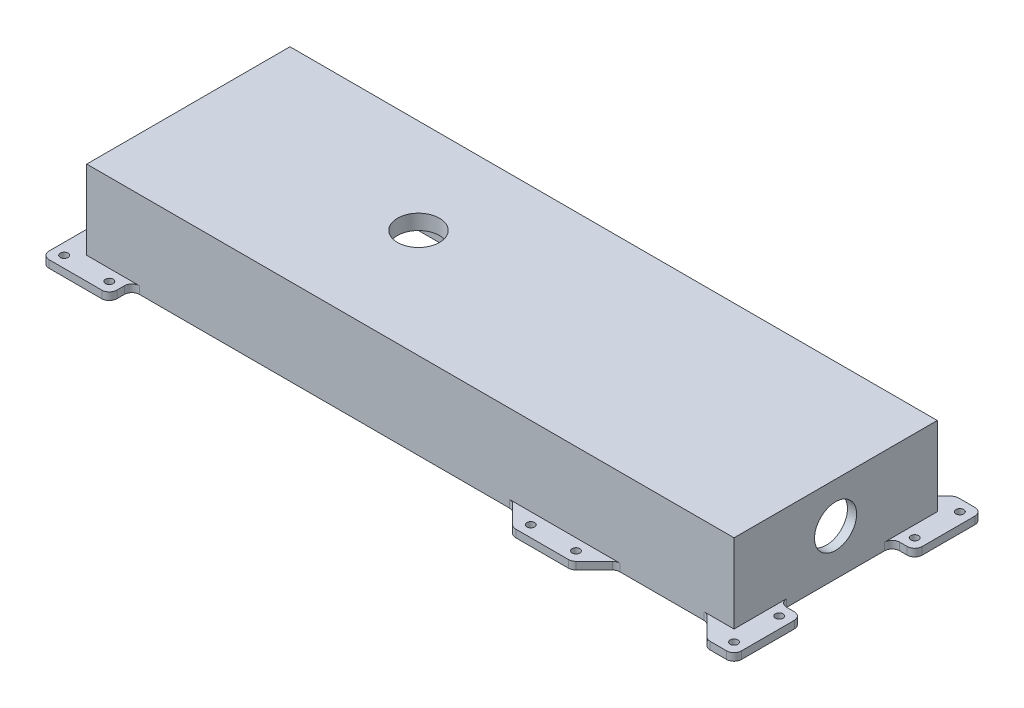
SolidWorks part; units mm, degrees
material "6061 Alloy"
ref_plane "Front Plane" through (0, 0, 0) normal (0, 0, 1) x (1, 0, 0)
ref_plane "Top Plane" through (0, 0, 0) normal (0, 1, 0) x (1, 0, 0)
ref_plane "Right Plane" through (0, 0, 0) normal (1, 0, 0) x (0, 0, -1)
sketch "Sketch1" plane through (0, 0, 0) normal (0, 1, 0) x (1, 0, 0)
  line L1 (-273.05, -85.725) -> (273.05, -85.725)
  line L2 (-273.05, -85.725) -> (-273.05, 85.725)
  line L3 (-273.05, 85.725) -> (273.05, 85.725)
  line L4 (273.05, -85.725) -> (273.05, 85.725)
  line L5 (-273.05, -85.725) -> (273.05, 85.725) construction
  line L6 (-273.05, 85.725) -> (273.05, -85.725) construction
  point P0 (0, 0)
  dimension "D1" = 546.1
  dimension "D2" = 171.45
extrude "Boss-Extrude1" add sketch "Sketch1" along normal blind 73.025
sketch "Sketch2" plane through (0, 0, 0) normal (0, -1, 0) x (1, 0, 0)
  line L0 (-220.7486, -78.0129) -> (-220.7486, -85.725) construction
  line L1 (273.05, -85.725) -> (-273.05, -85.725) construction
  line L2 (-265.3379, -33.4236) -> (-273.05, -33.4236) construction
  line L3 (-273.05, -85.725) -> (-273.05, 85.725) construction
  line L4 (220.7486, -78.0129) -> (220.7486, -85.725) construction
  line L5 (265.3379, -33.4236) -> (273.05, -33.4236) construction
  line L6 (273.05, 85.725) -> (273.05, -85.725) construction
  line L7 (-220.7486, 78.0129) -> (-220.7486, 85.725) construction
  line L8 (-273.05, 85.725) -> (273.05, 85.725) construction
  line L9 (-265.3379, 33.4236) -> (-273.05, 33.4236) construction
  line L10 (265.3379, 33.4236) -> (273.05, 33.4236) construction
  line L11 (220.7486, 78.0129) -> (220.7486, 85.725)
  line L18 (220.7486, 78.0129) -> (-220.7486, 78.0129)
  line L19 (265.3379, -33.4236) -> (265.3379, 33.4236)
  line L20 (-220.7486, -78.0129) -> (220.7486, -78.0129)
  line L21 (-265.3379, 33.4236) -> (-265.3379, -33.4236)
  arc A0 (265.3379, -33.4236) -> (220.7486, -78.0129) centre (220.7486, -33.4236) cw
  arc A1 (220.7486, 78.0129) -> (265.3379, 33.4236) centre (220.7486, 33.4236) cw
  arc A2 (-220.7486, 78.0129) -> (-265.3379, 33.4236) centre (-220.7486, 33.4236) ccw
  arc A3 (-220.7486, -78.0129) -> (-265.3379, -33.4236) centre (-220.7486, -33.4236) cw
  dimension "D2" = 44.5893
extrude "Cut-Extrude1" cut sketch "Sketch2" against normal offset from surface (60.325 mm away) 12.7 contours A1 L19 A0 L20 A3 L21 A2 L18 up to face at (0, 73.025, 0)
sketch "Sketch4" plane through (0, 60.325, 0) normal (0, -1, 0) x (1, 0, 0)
  line L0 (-265.3379, -6.35) -> (-265.3379, 6.35)
  line L2 (-265.3379, 33.4236) -> (-265.3379, -33.4236) construction
  line L3 (-265.3379, 6.35) -> (-96.9126, 6.35)
  line L4 (-96.9126, 6.35) -> (-96.9126, 78.0129)
  line L5 (-220.7486, 78.0129) -> (220.7486, 78.0129) construction
  line L6 (-96.9126, 78.0129) -> (-84.2126, 78.0129)
  line L7 (-84.2126, 78.0129) -> (-84.2126, 6.35)
  line L8 (-84.2126, 6.35) -> (84.2126, 6.35)
  line L9 (84.2126, 6.35) -> (84.2126, 78.0129)
  line L10 (84.2126, 78.0129) -> (96.9126, 78.0129)
  line L11 (96.9126, 78.0129) -> (96.9126, 6.35)
  line L12 (96.9126, 6.35) -> (265.3379, 6.35)
  line L13 (265.3379, 33.4236) -> (265.3379, -33.4236) construction
  line L14 (265.3379, 6.35) -> (265.3379, -6.35)
  line L15 (265.3379, -6.35) -> (96.9126, -6.35)
  line L16 (96.9126, -6.35) -> (96.9126, -78.0129)
  line L17 (220.7486, -78.0129) -> (-220.7486, -78.0129) construction
  line L18 (96.9126, -78.0129) -> (84.2126, -78.0129)
  line L19 (-220.7486, -78.0129) -> (220.7486, -78.0129) construction
  line L20 (84.2126, -78.0129) -> (84.2126, -6.35)
  line L21 (84.2126, -6.35) -> (-84.2126, -6.35)
  line L22 (-84.2126, -6.35) -> (-84.2126, -78.0129)
  line L23 (-84.2126, -78.0129) -> (-96.9126, -78.0129)
  line L24 (-96.9126, -78.0129) -> (-96.9126, -6.35)
  line L25 (-96.9126, -6.35) -> (-265.3379, -6.35)
  point P3 (-265.3379, 0)
  dimension "D1" = 12.7
extrude "Boss-Extrude3" [suppressed] add sketch "Sketch4" along normal blind 6.35
fillet "Fillet1" [suppressed] radius 19.05
sketch "Sketch5" plane through (0, 73.025, 0) normal (0, 1, 0) x (1, 0, 0)
  circle A0 centre (-84.7007, 5.8112) radius 17.7497
  circle A1 centre (-84.7007, 5.8112) radius 20.2897
  circle A2 centre (-84.7007, 5.8112) radius 20.2897 construction
  dimension "D1" = 0
  dimension "D2" = 2.54
extrude "Cut-Extrude2" cut sketch "Sketch5" against normal up to next
sketch "Sketch6" plane through (273.05, 0, 0) normal (1, 0, 0) x (0, 0, -1)
  circle A0 centre (-0.0776, 38.74) radius 17.7497
  circle A1 centre (-0.0776, 38.74) radius 20.2897
  circle A2 centre (-0.0776, 38.74) radius 20.2897 construction
  dimension "D1" = 0
  dimension "D2" = 2.54
extrude "Cut-Extrude3" cut sketch "Sketch6" against normal up to next
chamfer "Chamfer1" distance 0.635 8 edges at (252.278, 0, -64.953) (265.3379, 0, 0) (252.278, 0, 64.953) (0, 0, 78.0129) (-252.278, 0, 64.953) (0, 0, -78.0129) (-265.3379, 0, 0) (-252.278, 0, -64.953)
sketch "Sketch7" plane through (0, 0, 0) normal (0, -1, 0) x (1, 0, 0)
  line L0 (-273.05, -85.725) -> (-273.05, 85.725) construction
  line L1 (273.05, -85.725) -> (-273.05, -85.725) construction
  line L2 (273.05, 85.725) -> (273.05, -85.725) construction
  line L3 (-273.05, 85.725) -> (273.05, 85.725) construction
  line L4 (-273.05, -85.725) -> (-273.05, 85.725)
  line L5 (273.05, -85.725) -> (-273.05, -85.725)
  line L6 (273.05, 85.725) -> (273.05, -85.725)
  line L7 (-273.05, 85.725) -> (273.05, 85.725)
  line L36 (-228.6, -85.725) -> (83.6395, -85.725)
  line L37 (88.1296, -87.5849) -> (103.4599, -102.9151)
  line L38 (107.95, -104.775) -> (152.4, -104.775)
  line L39 (156.8901, -102.9151) -> (172.2204, -87.5849)
  line L40 (176.7105, -85.725) -> (247.65, -85.725)
  line L41 (252.1401, -87.5849) -> (267.4704, -102.9151)
  line L42 (271.9605, -104.775) -> (285.75, -104.775)
  line L43 (292.1, -98.425) -> (292.1, -53.975)
  line L44 (285.75, -47.625) -> (279.4, -47.625)
  line L45 (273.05, -41.275) -> (273.05, 41.275)
  line L46 (279.4, 47.625) -> (285.75, 47.625)
  line L47 (292.1, 53.975) -> (292.1, 98.425)
  line L48 (285.75, 104.775) -> (271.9605, 104.775)
  line L49 (267.4704, 102.9151) -> (252.1401, 87.5849)
  line L50 (247.65, 85.725) -> (176.7105, 85.725)
  line L51 (172.2204, 87.5849) -> (156.8901, 102.9151)
  line L52 (152.4, 104.775) -> (107.95, 104.775)
  line L53 (103.4599, 102.9151) -> (88.1296, 87.5849)
  line L54 (83.6395, 85.725) -> (-228.6, 85.725)
  line L55 (-234.95, 92.075) -> (-234.95, 98.425)
  line L56 (-241.3, 104.775) -> (-285.75, 104.775)
  line L57 (-292.1, 98.425) -> (-292.1, 53.975)
  line L58 (-285.75, 47.625) -> (-279.4, 47.625)
  line L59 (-273.05, 41.275) -> (-273.05, -41.275)
  line L60 (-279.4, -47.625) -> (-285.75, -47.625)
  line L61 (-292.1, -53.975) -> (-292.1, -98.425)
  line L62 (-285.75, -104.775) -> (-241.3, -104.775)
  line L63 (-234.95, -98.425) -> (-234.95, -92.075)
  line L64 (-228.6, -85.725) -> (83.6395, -85.725)
  line L65 (88.1296, -87.5849) -> (103.4599, -102.9151)
  line L66 (107.95, -104.775) -> (152.4, -104.775)
  line L67 (156.8901, -102.9151) -> (172.2204, -87.5849)
  line L68 (176.7105, -85.725) -> (247.65, -85.725)
  line L69 (252.1401, -87.5849) -> (267.4704, -102.9151)
  line L70 (271.9605, -104.775) -> (285.75, -104.775)
  line L71 (292.1, -98.425) -> (292.1, -53.975)
  line L72 (285.75, -47.625) -> (279.4, -47.625)
  line L73 (273.05, -41.275) -> (273.05, 41.275)
  line L74 (279.4, 47.625) -> (285.75, 47.625)
  line L75 (292.1, 53.975) -> (292.1, 98.425)
  line L76 (285.75, 104.775) -> (271.9605, 104.775)
  line L77 (267.4704, 102.9151) -> (252.1401, 87.5849)
  line L78 (247.65, 85.725) -> (176.7105, 85.725)
  line L79 (172.2204, 87.5849) -> (156.8901, 102.9151)
  line L80 (152.4, 104.775) -> (107.95, 104.775)
  line L81 (103.4599, 102.9151) -> (88.1296, 87.5849)
  line L82 (83.6395, 85.725) -> (-228.6, 85.725)
  line L83 (-234.95, 92.075) -> (-234.95, 98.425)
  line L84 (-241.3, 104.775) -> (-285.75, 104.775)
  line L85 (-292.1, 98.425) -> (-292.1, 53.975)
  line L86 (-285.75, 47.625) -> (-279.4, 47.625)
  line L87 (-273.05, 41.275) -> (-273.05, -41.275)
  line L88 (-279.4, -47.625) -> (-285.75, -47.625)
  line L89 (-292.1, -53.975) -> (-292.1, -98.425)
  line L90 (-285.75, -104.775) -> (-241.3, -104.775)
  line L91 (-234.95, -98.425) -> (-234.95, -92.075)
  circle A0 centre (111.125, 95.25) radius 3.2639 construction
  circle A1 centre (149.225, 95.25) radius 3.2639 construction
  circle A2 centre (282.575, 95.25) radius 3.2639 construction
  circle A3 centre (282.575, 57.15) radius 3.2639 construction
  circle A4 centre (282.575, -57.15) radius 3.2639 construction
  circle A5 centre (282.575, -95.25) radius 3.2639 construction
  circle A6 centre (149.225, -95.25) radius 3.2639 construction
  circle A7 centre (111.125, -95.25) radius 3.2639 construction
  circle A8 centre (-244.475, -95.25) radius 3.2639 construction
  circle A9 centre (-282.575, -95.25) radius 3.2639 construction
  circle A10 centre (-282.575, -57.15) radius 3.2639 construction
  circle A11 centre (-282.575, 57.15) radius 3.2639 construction
  circle A12 centre (-244.475, 95.25) radius 3.2639 construction
  circle A13 centre (-282.575, 95.25) radius 3.2639 construction
  circle A14 centre (111.125, 95.25) radius 3.2639
  circle A15 centre (149.225, 95.25) radius 3.2639
  circle A16 centre (282.575, 95.25) radius 3.2639
  circle A17 centre (282.575, 57.15) radius 3.2639
  circle A18 centre (282.575, -57.15) radius 3.2639
  circle A19 centre (282.575, -95.25) radius 3.2639
  circle A20 centre (149.225, -95.25) radius 3.2639
  circle A21 centre (111.125, -95.25) radius 3.2639
  circle A22 centre (-244.475, -95.25) radius 3.2639
  circle A23 centre (-282.575, -95.25) radius 3.2639
  circle A24 centre (-282.575, -57.15) radius 3.2639
  circle A25 centre (-282.575, 57.15) radius 3.2639
  circle A26 centre (-244.475, 95.25) radius 3.2639
  circle A27 centre (-282.575, 95.25) radius 3.2639
  arc A28 (-228.6, -85.725) -> (-234.95, -92.075) centre (-228.6, -92.075) ccw
  arc A29 (88.1296, -87.5849) -> (83.6395, -85.725) centre (83.6395, -92.075) ccw
  arc A30 (103.4599, -102.9151) -> (107.95, -104.775) centre (107.95, -98.425) ccw
  arc A31 (152.4, -104.775) -> (156.8901, -102.9151) centre (152.4, -98.425) ccw
  arc A32 (176.7105, -85.725) -> (172.2204, -87.5849) centre (176.7105, -92.075) ccw
  arc A33 (252.1401, -87.5849) -> (247.65, -85.725) centre (247.65, -92.075) ccw
  arc A34 (267.4704, -102.9151) -> (271.9605, -104.775) centre (271.9605, -98.425) ccw
  arc A35 (285.75, -104.775) -> (292.1, -98.425) centre (285.75, -98.425) ccw
  arc A36 (292.1, -53.975) -> (285.75, -47.625) centre (285.75, -53.975) ccw
  arc A37 (273.05, -41.275) -> (279.4, -47.625) centre (279.4, -41.275) ccw
  arc A38 (279.4, 47.625) -> (273.05, 41.275) centre (279.4, 41.275) ccw
  arc A39 (285.75, 47.625) -> (292.1, 53.975) centre (285.75, 53.975) ccw
  arc A40 (292.1, 98.425) -> (285.75, 104.775) centre (285.75, 98.425) ccw
  arc A41 (271.9605, 104.775) -> (267.4704, 102.9151) centre (271.9605, 98.425) ccw
  arc A42 (247.65, 85.725) -> (252.1401, 87.5849) centre (247.65, 92.075) ccw
  arc A43 (172.2204, 87.5849) -> (176.7105, 85.725) centre (176.7105, 92.075) ccw
  arc A44 (156.8901, 102.9151) -> (152.4, 104.775) centre (152.4, 98.425) ccw
  arc A45 (107.95, 104.775) -> (103.4599, 102.9151) centre (107.95, 98.425) ccw
  arc A46 (83.6395, 85.725) -> (88.1296, 87.5849) centre (83.6395, 92.075) ccw
  arc A47 (-234.95, 92.075) -> (-228.6, 85.725) centre (-228.6, 92.075) ccw
  arc A48 (-234.95, 98.425) -> (-241.3, 104.775) centre (-241.3, 98.425) ccw
  arc A49 (-285.75, 104.775) -> (-292.1, 98.425) centre (-285.75, 98.425) ccw
  arc A50 (-292.1, 53.975) -> (-285.75, 47.625) centre (-285.75, 53.975) ccw
  arc A51 (-273.05, 41.275) -> (-279.4, 47.625) centre (-279.4, 41.275) ccw
  arc A52 (-279.4, -47.625) -> (-273.05, -41.275) centre (-279.4, -41.275) ccw
  arc A53 (-285.75, -47.625) -> (-292.1, -53.975) centre (-285.75, -53.975) ccw
  arc A54 (-292.1, -98.425) -> (-285.75, -104.775) centre (-285.75, -98.425) ccw
  arc A55 (-241.3, -104.775) -> (-234.95, -98.425) centre (-241.3, -98.425) ccw
  arc A56 (-228.6, -85.725) -> (-234.95, -92.075) centre (-228.6, -92.075) ccw
  arc A57 (88.1296, -87.5849) -> (83.6395, -85.725) centre (83.6395, -92.075) ccw
  arc A58 (103.4599, -102.9151) -> (107.95, -104.775) centre (107.95, -98.425) ccw
  arc A59 (152.4, -104.775) -> (156.8901, -102.9151) centre (152.4, -98.425) ccw
  arc A60 (176.7105, -85.725) -> (172.2204, -87.5849) centre (176.7105, -92.075) ccw
  arc A61 (252.1401, -87.5849) -> (247.65, -85.725) centre (247.65, -92.075) ccw
  arc A62 (267.4704, -102.9151) -> (271.9605, -104.775) centre (271.9605, -98.425) ccw
  arc A63 (285.75, -104.775) -> (292.1, -98.425) centre (285.75, -98.425) ccw
  arc A64 (292.1, -53.975) -> (285.75, -47.625) centre (285.75, -53.975) ccw
  arc A65 (273.05, -41.275) -> (279.4, -47.625) centre (279.4, -41.275) ccw
  arc A66 (279.4, 47.625) -> (273.05, 41.275) centre (279.4, 41.275) ccw
  arc A67 (285.75, 47.625) -> (292.1, 53.975) centre (285.75, 53.975) ccw
  arc A68 (292.1, 98.425) -> (285.75, 104.775) centre (285.75, 98.425) ccw
  arc A69 (271.9605, 104.775) -> (267.4704, 102.9151) centre (271.9605, 98.425) ccw
  arc A70 (247.65, 85.725) -> (252.1401, 87.5849) centre (247.65, 92.075) ccw
  arc A71 (172.2204, 87.5849) -> (176.7105, 85.725) centre (176.7105, 92.075) ccw
  arc A72 (156.8901, 102.9151) -> (152.4, 104.775) centre (152.4, 98.425) ccw
  arc A73 (107.95, 104.775) -> (103.4599, 102.9151) centre (107.95, 98.425) ccw
  arc A74 (83.6395, 85.725) -> (88.1296, 87.5849) centre (83.6395, 92.075) ccw
  arc A75 (-234.95, 92.075) -> (-228.6, 85.725) centre (-228.6, 92.075) ccw
  arc A76 (-234.95, 98.425) -> (-241.3, 104.775) centre (-241.3, 98.425) ccw
  arc A77 (-285.75, 104.775) -> (-292.1, 98.425) centre (-285.75, 98.425) ccw
  arc A78 (-292.1, 53.975) -> (-285.75, 47.625) centre (-285.75, 53.975) ccw
  arc A79 (-273.05, 41.275) -> (-279.4, 47.625) centre (-279.4, 41.275) ccw
  arc A80 (-279.4, -47.625) -> (-273.05, -41.275) centre (-279.4, -41.275) ccw
  arc A81 (-285.75, -47.625) -> (-292.1, -53.975) centre (-285.75, -53.975) ccw
  arc A82 (-292.1, -98.425) -> (-285.75, -104.775) centre (-285.75, -98.425) ccw
  arc A83 (-241.3, -104.775) -> (-234.95, -98.425) centre (-241.3, -98.425) ccw
  line M69 (273.05, -85.725) -> (273.05, 85.725)
  line M70 (273.05, 85.725) -> (-273.05, 85.725)
  line M71 (-273.05, 85.725) -> (-273.05, -85.725)
  line M72 (-273.05, -85.725) -> (273.05, -85.725)
  dimension "D1" = 0
extrude "Boss-Extrude4" add sketch "Sketch7" against normal blind 6.35 contours A79 A75 L83 A76 L84 A77 L85 A78 L86 A27 A26 A25 M71 M70 | A74 A71 L79 A72 L80 A73 L81 A14 A15 M70 | A70 A66 L74 A67 L75 A68 L76 A69 L77 A17 A16 M70 M69 | A65 A61 L69 A62 L70 A63 L71 A64 L72 A18 A19 M69 M72 | A60 A57 L65 A58 L66 A59 L67 A21 A20 M72 | L90 A83 L91 A56 A80 L88 A81 L89 A82 A24 A23 A22 M72 M71
equation "\"oring.277.ID\"= 15.955in"
equation "\"oring.277.A\"= 16.250in"
equation "\"oring.277.A1\"= 16.222in"
equation "\"oring.277.B\"= 16.000in"
equation "\"oring.277.B1\"= 16.028in"
equation "\"oring.277.C\"= 16.247in"
equation "\"oring.277.D\"= 16.003in"
equation "\"oring.277.G\"= 0.187in"
equation "\"D1@Sketch2\" = ( \"oring.282.A\" + \"anodize.add\" * 2 ) * PI"
equation "\"D2@Sketch2\"= 12 * \"oring.282.W\" + ( \"oring.282.C.factor\" - \"oring.282.B1\" ) / 2"
equation "\"oring.277.W\"= 0.139in"
equation "\"anodize.add\"= 0.001in"
equation "\"c.factor\"= 0.00271"
equation "\"oring.277.C.factor\"= \"oring.277.C\" - \"oring.277.C\" * \"c.factor\""
equation "\"oring.selected\"= \"277\""
equation "\"oring.282.ID\"= 15.955in"
equation "\"oring.282.A\"= 16.250in"
equation "\"oring.282.A1\"= 16.222in"
equation "\"oring.282.B\"= 16.000in"
equation "\"oring.282.B1\"= 16.028in"
equation "\"oring.282.C\"= 16.247in"
equation "\"oring.282.D\"= 16.003in"
equation "\"oring.282.G\"= 0.187in"
equation "\"oring.282.W\"= 0.139in"
equation "\"oring.282.C.factor\"= \"oring.282.C\" - \"oring.282.C\" * \"c.factor\""
